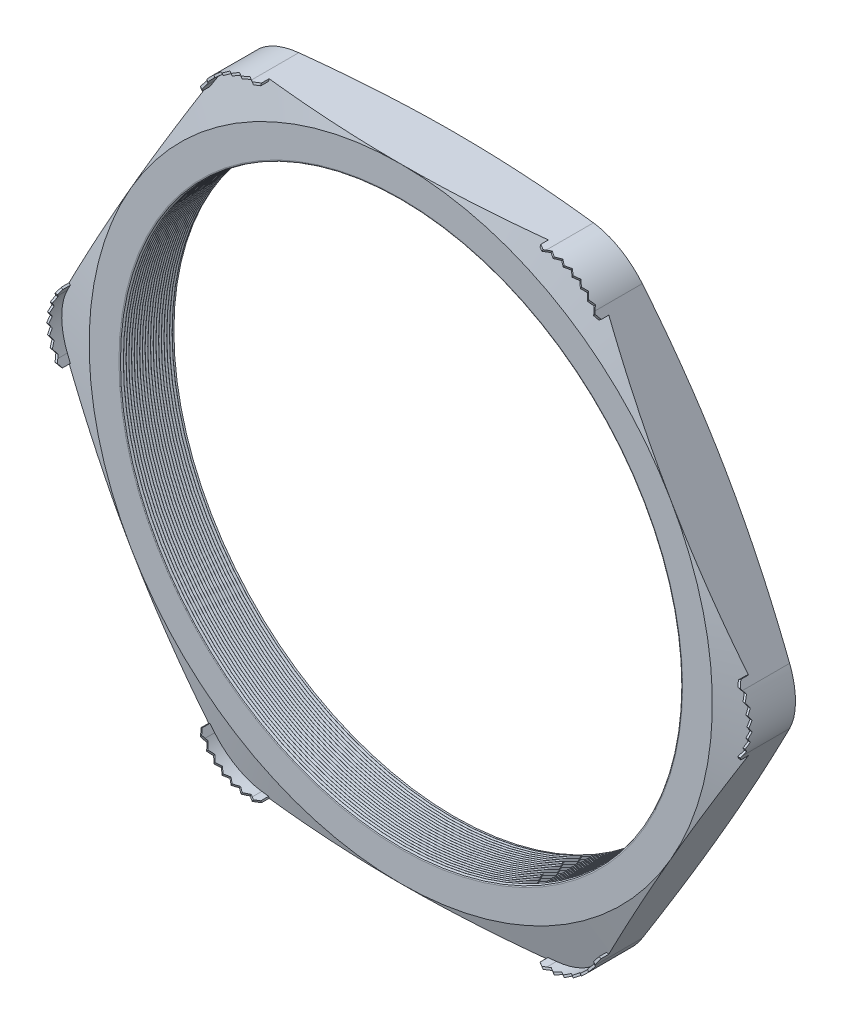
SolidWorks part; units mm, degrees
ref_plane "Front Plane" through (0, 0, 0) normal (0, 0, 1) x (1, 0, 0)
ref_plane "Top Plane" through (0, 0, 0) normal (0, 1, 0) x (1, 0, 0)
ref_plane "Right Plane" through (0, 0, 0) normal (1, 0, 0) x (0, 0, -1)
sketch "Sketch1" plane through (0, 0, 0) normal (0, 0, 1) x (1, 0, 0)
  line L1 (-40.4746, 0) -> (-20.2373, -35.052)
  line L2 (-20.2373, -35.052) -> (20.2373, -35.052)
  line L3 (20.2373, -35.052) -> (40.4746, 0)
  line L4 (40.4746, 0) -> (20.2373, 35.052)
  line L5 (20.2373, 35.052) -> (-20.2373, 35.052)
  line L6 (-20.2373, 35.052) -> (-40.4746, 0)
  circle A0 centre (0, 0) radius 35.052 construction
  circle A1 centre (0, 0) radius 31.496
  dimension "TS" = 62.992
  dimension "H" = 70.104
extrude "Extrude1" add sketch "Sketch1" along normal blind 6.096
fillet "Fillet1" radius 6.35 6 edges at (-20.2373, 35.052, 3.048) (-40.4746, 0, 3.048) (-20.2373, -35.052, 3.048) (20.2373, -35.052, 3.048) (40.4746, 0, 3.048) (20.2373, 35.052, 3.048)
sketch "Sketch2" plane through (0, 0, 6.096) normal (0, 0, 1) x (1, 0, 0)
  line L0 (-16.5711, 35.052) -> (-15.7075, 35.052)
  line L1 (16.5711, 35.052) -> (-16.5711, 35.052) construction
  line L2 (-22.0704, 31.877) -> (-22.5022, 31.1291)
  line L3 (-22.0704, 31.877) -> (-38.6415, 3.175) construction
  line L4 (-16.5711, 34.8234) -> (-15.7075, 34.8234)
  line L5 (-21.8724, 31.7627) -> (-22.3042, 31.0148)
  line L6 (-22.5022, 31.1291) -> (-22.3042, 31.0148)
  line L7 (-15.7075, 35.052) -> (-15.7075, 34.8234)
  arc A0 (-16.5711, 34.8234) -> (-21.8724, 31.7627) centre (-16.5711, 28.702) ccw
  arc A1 (-16.5711, 35.052) -> (-22.0704, 31.877) centre (-16.5711, 28.702) ccw construction
  arc A4 (-16.5711, 35.052) -> (-22.0704, 31.877) centre (-16.5711, 28.702) ccw
  dimension "D1" = 0.8636
  dimension "D2" = 0.8636
  dimension "OFFSET" = 0.2286
fillet "Fillet3" radius 0.2032 2 edges at (31.496, 0, 0) (31.496, 0, 6.096)
sketch "Sketch3" plane through (0, 0, 0) normal (0, 1, 0) x (1, 0, 0)
  line L0 (-31.496, -6.096) -> (-31.496, -5.8027)
  line L2 (-31.496, -5.8027) -> (-31.75, -5.9494)
  line L3 (-31.75, -5.9494) -> (-31.496, -6.096)
  line L4 (-31.496, -0.2032) -> (-31.496, -5.8928) construction
  line L5 (-22.0704, -6.096) -> (-38.6415, -6.096) construction
  dimension "D1" = 60
  dimension "D2" = 60
  dimension "D3" = 0.254
revolve "Cut-Revolve1" cut sketch "Sketch3" angle 360 about axis through (0, 0, 6.096) along (0, 0, -1)
pattern_linear "LPattern1" count 20 spacing 0.3048 along (0, 0, -1) of "Cut-Revolve1"
sketch "Sketch4" plane through (0, 0, 0) normal (0, 0, -1) x (-1, 0, 0)
  line L0 (-38.6415, 3.175) -> (-22.0704, 31.877) construction
  circle A0 centre (0, 0) radius 35.052
extrude "Cut-Extrude1" cut sketch "Sketch4" against normal through all draft 75 flip side to cut
sketch "Sketch5" plane through (0, 0, 6.096) normal (0, 0, 1) x (1, 0, 0)
  line L0 (16.5711, 35.052) -> (-16.5711, 35.052) construction
  circle A0 centre (0, 0) radius 35.052
extrude "Cut-Extrude2" cut sketch "Sketch5" against normal through all draft 75 flip side to cut
extrude "Extrude2" add sketch "Sketch2" along normal blind 0.9398 and the other way up to next
ref_plane "Plane1" through (-19.0059, 32.9191, 0) normal (0.5, -0.866, 0) x (0.866, 0.5, 0)
sketch "Sketch7" plane through (-19.0059, 32.9191, 0) normal (0.5, -0.866, 0) x (0.866, 0.5, 0)
  line L0 (-3.9229, 6.049) -> (-3.3641, 6.4437)
  line L1 (-3.9229, 5.1961) -> (-3.9229, 7.0358) construction
  line L2 (0, 1.3136) -> (0, 4.0135) construction
  line L4 (-3.3641, 6.4437) -> (-2.8053, 6.049)
  line L5 (-1.1176, 6.4437) -> (-0.5588, 6.049)
  line L6 (-2.2352, 6.4437) -> (-1.6764, 6.049)
  line L7 (-0.5588, 6.049) -> (0, 6.4437)
  line L8 (0, 6.4437) -> (0.5588, 6.049)
  line L10 (1.1176, 6.4437) -> (1.6764, 6.049)
  line L11 (2.2352, 6.4437) -> (2.794, 6.049)
  line L12 (-2.8053, 6.049) -> (-2.2352, 6.4437)
  line L13 (-1.6764, 6.049) -> (-1.1176, 6.4437)
  line L14 (0.5588, 6.049) -> (1.1176, 6.4437)
  line L15 (3.3641, 6.4437) -> (3.9229, 6.049)
  line L16 (3.9229, 5.1961) -> (3.9229, 7.0358) construction
  line L17 (-3.9229, 6.049) -> (-3.9229, 7.0358)
  line L19 (-3.9229, 7.0358) -> (3.9229, 7.0358)
  line L20 (3.9229, 7.0358) -> (3.9229, 6.049)
  line L23 (1.6764, 6.049) -> (2.2352, 6.4437)
  line L25 (2.794, 6.049) -> (3.3641, 6.4437)
  dimension "D1" = 0.9868
  dimension "D2" = 0.5921
  dimension "D3" = 0.5588
extrude "Cut-Extrude4" cut sketch "Sketch7" against normal through all
pattern_circular "CirPattern1" count 6 over 360 about axis through (0, 0, 0) along (0, 0, 1) of "Extrude2"
pattern_circular "CirPattern2" count 6 over 360 about axis through (0, 0, 0) along (0, 0, 1) of "Cut-Extrude4"
